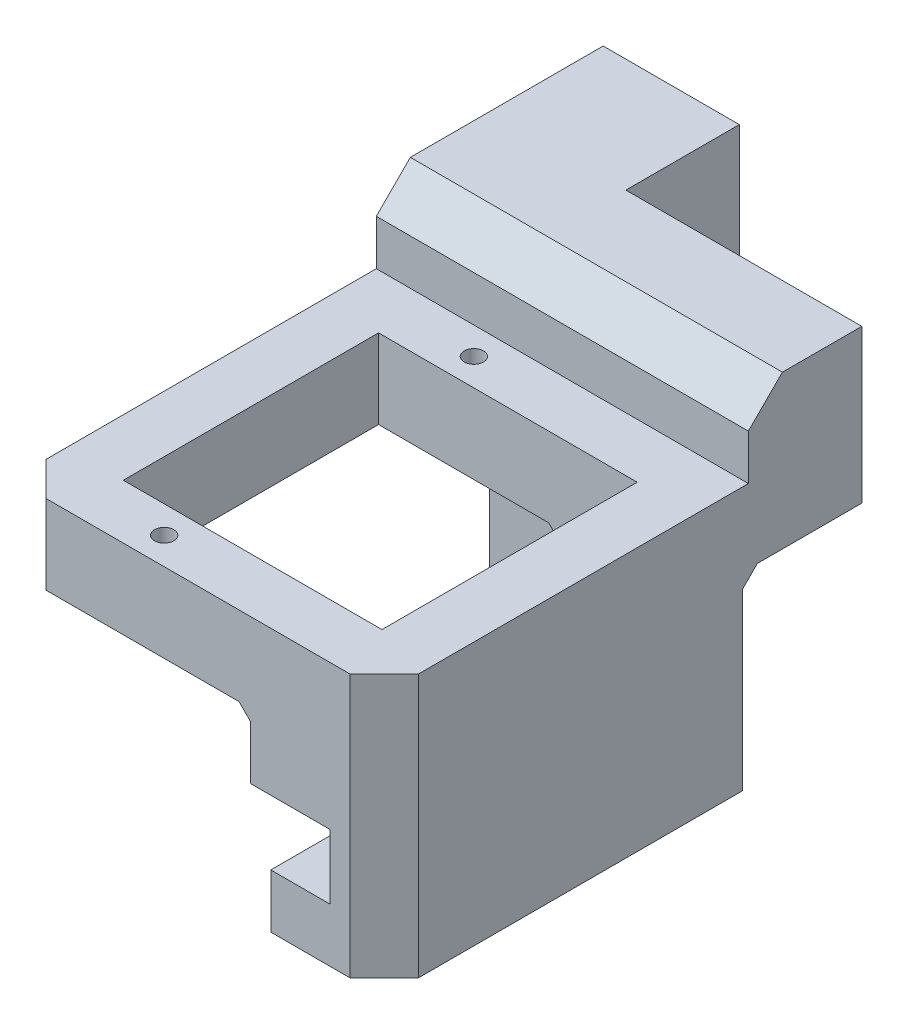
SolidWorks part; units mm, degrees
ref_plane "Front Plane" through (0, 0, 0) normal (0, 0, 1) x (1, 0, 0)
ref_plane "Top Plane" through (0, 0, 0) normal (0, 1, 0) x (1, 0, 0)
ref_plane "Right Plane" through (0, 0, 0) normal (1, 0, 0) x (0, 0, -1)
sketch "Sketch1" plane through (0, 0, 0) normal (0, 1, 0) x (1, 0, 0)
  line L0 (0, 0) -> (28.7191, 0) construction
  line L1 (0, -16.05) -> (0, 16.05)
  line L2 (0, 16.05) -> (17, 16.05)
  line L3 (17, 16.05) -> (17, 11.25)
  line L4 (17, 11.25) -> (5, 11.25)
  line L5 (5, 11.25) -> (5, -11.25)
  line L6 (17, 13.65) -> (11, 13.65) construction
  line L7 (17, -13.65) -> (11, -13.65) construction
  line L8 (17, -11.25) -> (5, -11.25)
  line L9 (17, -16.05) -> (17, -11.25)
  line L10 (0, -16.05) -> (17, -16.05)
  circle A0 centre (11, 13.65) radius 0.85
  circle A1 centre (11, -13.65) radius 0.85
  point P13 (5, 0)
  dimension "D5" = 1.7
  dimension "D6" = 6
  dimension "D1" = 12
  dimension "D2" = 5
  dimension "D3" = 4.8
  dimension "D4" = 11.25
extrude "Boss-Extrude1" add sketch "Sketch1" along normal blind 7
sketch "Sketch2" plane through (0, 0, 0) normal (0, -1, 0) x (1, 0, 0)
  line L0 (17, 11.25) -> (27.8, 11.25)
  line L1 (27.8, 11.25) -> (27.8, -11.25)
  line L2 (27.8, -11.25) -> (17, -11.25)
  line L3 (17, 16.05) -> (32.8, 16.05)
  line L4 (32.8, 16.05) -> (32.8, -16.05)
  line L5 (17, -16.05) -> (32.8, -16.05)
  line L6 (17, 16.05) -> (17, 11.25)
  line L7 (17, -16.05) -> (17, -11.25)
  dimension "D1" = 10.8
  dimension "D2" = 5
extrude "Boss-Extrude2" add sketch "Sketch2" along normal blind 11.2 and the other way blind 7
sketch "Sketch3" plane through (0, 0, 16.05) normal (0, 0, 1) x (1, 0, 0)
  line L0 (0, 0) -> (17, 0) construction
  line L1 (17, -11.2) -> (28, -11.2)
  line L2 (17, -11.2) -> (17, 0)
  line L3 (17, 0) -> (28, 0)
  line L4 (28, -11.2) -> (28, 0)
  dimension "D1" = 11
extrude "Cut-Extrude1" cut sketch "Sketch3" against normal blind 42
sketch "Sketch4" plane through (0, -11.2, 0) normal (0, -1, 0) x (1, 0, 0)
  line L0 (28, -16.05) -> (0, -16.05) construction
  line L1 (32.8, 16.05) -> (22.8, 16.05)
  line L2 (32.8, 16.05) -> (32.8, -16.05)
  line L3 (32.8, -16.05) -> (22.8, -16.05)
  line L4 (22.8, 16.05) -> (22.8, -16.05)
  dimension "D1" = 10
extrude "Boss-Extrude3" add sketch "Sketch4" along normal blind 5
sketch "Sketch5" plane through (0, 0, 16.05) normal (0, 0, 1) x (1, 0, 0)
  line L1 (28, 0) -> (21, 0)
  line L2 (28, 0) -> (28, -6)
  line L3 (28, -6) -> (21, -6)
  line L4 (21, 0) -> (21, -6)
  dimension "D1" = 6
  dimension "D2" = 7
extrude "Boss-Extrude4" add sketch "Sketch5" against normal up to surface (32.1 mm away) up to face at (20.9, -5.1, -16.05)
sketch "Sketch6" plane through (0, 0, -16.05) normal (0, 0, -1) x (-1, 0, 0)
  line L0 (0, 7) -> (0, 0) construction
  line L1 (-32.8, 7) -> (0, 7)
  line L2 (-32.8, 7) -> (-32.8, 14)
  line L3 (-32.8, 14) -> (0, 14)
  line L4 (0, 7) -> (0, 14)
  dimension "D1" = 7
extrude "Boss-Extrude5" add sketch "Sketch6" along normal blind 10 separate body contours L3 L4 L1 L2
sketch "Sketch7" plane through (0, 0, 0) normal (-1, 0, 0) x (0, 0, 1)
  line L0 (-16.05, 7) -> (-16.05, 0)
  line L1 (-16.05, 0) -> (-26.05, 7)
  line L2 (-26.05, 7) -> (-16.05, 7)
extrude "Boss-Extrude6" [suppressed] add sketch "Sketch7" against normal up to surface (32.8 mm away)
sketch "Sketch8" plane through (0, 0, 0) normal (-1, 0, 0) x (0, 0, 1)
  line L1 (-26.05, 7) -> (-16.05, 7)
  line L2 (-26.05, 7) -> (-26.05, 0)
  line L3 (-26.05, 0) -> (-16.05, 0)
  line L4 (-16.05, 7) -> (-16.05, 0)
extrude "Boss-Extrude7" add sketch "Sketch8" against normal up to surface (32.8 mm away) up to face at (32.8, 10.5, -21.05)
sketch "Sketch9" plane through (0, 0, -26.05) normal (0, 0, -1) x (-1, 0, 0)
  line L0 (-28, -8.57) -> (0, -8.57) construction
  line L2 (0, -8.57) -> (0, 0) construction
  line L3 (0, 14) -> (0, 0) construction
  line L5 (-22.8, -11.2) -> (-28, -11.2) construction
  circle A0 centre (-23.7994, -8.57) radius 5.85
  circle A1 centre (-23.7994, -8.57) radius 10
  dimension "D1" = 11.7
  dimension "D2" = 20
  dimension "D3" = 23.7994
  dimension "D4" = 2.63
extrude "Boss-Extrude8" [suppressed] add sketch "Sketch9" along normal blind 15
sketch "Sketch10" [suppressed] plane through (0, 0, 0) normal (-1, 0, 0) x (0, 0, 1)
  line L0 (-31.05, 14) -> (-16.05, 14) construction
  line L1 (-31.05, 0) -> (-46.05, 0)
  line L2 (-31.05, 0) -> (-31.05, 14)
  line L3 (-31.05, 14) -> (-46.05, 14)
  line L4 (-46.05, 0) -> (-46.05, 14)
  line L5 (-46.05, 1.4) -> (-46.05, -18.6) construction
sketch "Sketch11" [suppressed] plane through (32.8, 0, 0) normal (1, 0, 0) x (0, 0, -1)
  line L0 (36.05, -18.57) -> (36.05, 1.43) construction
  line L1 (21.05, 14) -> (36.05, 14)
  line L2 (21.05, 14) -> (21.05, 0)
  line L3 (21.05, 0) -> (36.05, 0)
  line L4 (36.05, 14) -> (36.05, 0)
  line L5 (21.05, 0) -> (16.05, 0) construction
extrude "Boss-Extrude9" [suppressed] add sketch "Sketch11" against normal blind 18
fillet "Fillet1" [suppressed] radius 3
chamfer "Chamfer1" [suppressed] distance 15 angle 45
chamfer "Chamfer2" distance 1 angle 45 1 edges at (26.9, 0, -16.05)
chamfer "Chamfer3" distance 3 angle 45 2 edges at (32.8, -4.6, 16.05) (0, 3.5, 16.05)
chamfer "Chamfer4" distance 3 angle 45 1 edges at (16.4, 14, -16.05)
chamfer "Chamfer5" [suppressed] distance 0.5 angle 45
chamfer "Chamfer6" [suppressed] distance 0.5 angle 45
chamfer "Chamfer7" [suppressed] distance 2 angle 45
chamfer "Chamfer8" distance 0.5 angle 45 4 edges at (32.8, 0, -21.55) (32.8, -0.5, -16.55) (32.8, -8.6, -16.05) (27.8, -16.2, -16.05)
chamfer "Chamfer9" distance 1 angle 45 2 edges at (21, 0, -14.15) (21, 0, 13.65)
sketch "Sketch12" [suppressed] plane through (0, 0, -26.05) normal (0, 0, -1) x (-1, 0, 0)
  line L1 (0, 0) -> (-40, 0)
  line L2 (0, 0) -> (0, 21.7546)
  line L3 (0, 21.7546) -> (-40, 21.7546)
  line L4 (-40, 0) -> (-40, 21.7546)
  dimension "D1" = 40
sketch "Sketch13" plane through (0, 0, -26.05) normal (0, 0, -1) x (-1, 0, 0)
  line L0 (-37.8, -8.57) -> (0, -8.57) construction
  line L1 (-37.8, -21.07) -> (-37.8, 3.93) construction
  line L4 (0, 14) -> (-12, 14)
  line L5 (0, 14) -> (0, -31.14)
  line L6 (0, -31.14) -> (-12, -31.14)
  line L7 (-12, 14) -> (-12, -31.14)
  dimension "D1" = 12
extrude "Boss-Extrude10" add sketch "Sketch13" along normal blind 10
sketch "Sketch14" plane through (0, 0, -36.05) normal (0, 0, -1) x (-1, 0, 0)
  line L0 (-12, -8.57) -> (0, -8.57) construction
  line L1 (-12, 14) -> (-12, -31.14) construction
  line L2 (0, -31.14) -> (0, 14) construction
  line L3 (-6, -8.57) -> (-6, 1.43) construction
  circle A0 centre (-6, 1.43) radius 2.05
  circle A1 centre (-6, -18.57) radius 2.05
  dimension "D1" = 4.1
  dimension "D2" = 10
extrude "Cut-Extrude2" cut sketch "Sketch14" against normal blind 5
sketch "Sketch15" plane through (0, 0, 16.05) normal (0, 0, 1) x (1, 0, 0)
  line L0 (28, -8.6) -> (20.1442, -8.6) construction
  line L1 (28, -11.2) -> (28, -6) construction
  line L2 (28, -11.2) -> (28, -11.45)
  line L3 (21, -6) -> (28, -6)
  line L4 (21, -6) -> (21, -5.75)
  line L5 (21, -5.75) -> (28, -5.75)
  line L6 (28, -6) -> (28, -5.75)
  line L7 (21, -11.45) -> (28, -11.45)
  line L8 (21, -11.2) -> (21, -11.45)
  line L9 (21, -11.2) -> (28, -11.2)
  dimension "D1" = 0.25
extrude "Cut-Extrude3" cut sketch "Sketch15" against normal blind 39
